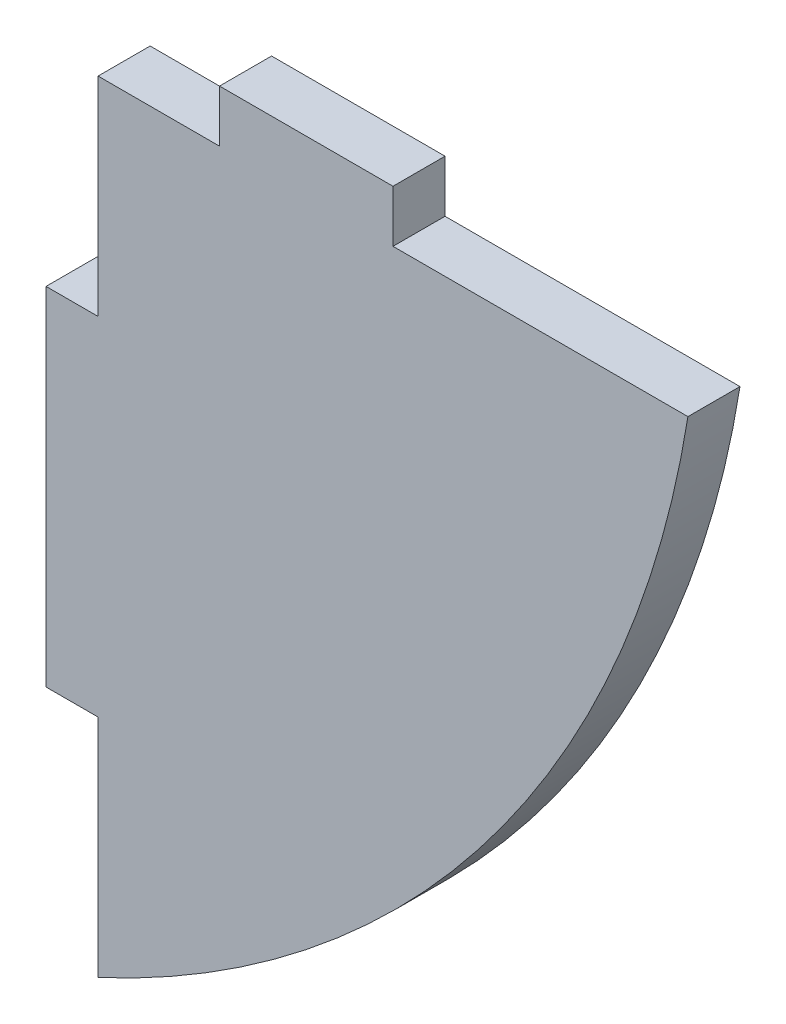
SolidWorks part; units mm, degrees
ref_plane "前视基准面" through (0, 0, 0) normal (0, 0, 1) x (1, 0, 0)
ref_plane "上视基准面" through (0, 0, 0) normal (0, 1, 0) x (1, 0, 0)
ref_plane "右视基准面" through (0, 0, 0) normal (1, 0, 0) x (0, 0, -1)
sketch "草图2" plane through (0, 0, 0) normal (0, 0, 1) x (1, 0, 0)
  line L0 (0, 45) -> (0, 33)
  line L1 (0, -55) -> (0, 55) construction
  line L2 (0, 45) -> (7, 45)
  line L3 (7, 45) -> (7, 48)
  line L4 (7, 48) -> (17, 48)
  line L5 (17, 48) -> (17, 45)
  line L6 (0, 33) -> (-3, 33)
  line L7 (-3, 33) -> (-3, 13)
  line L8 (-3, 13) -> (0, 13)
  line L9 (0, 13) -> (0, 0)
  line L10 (17, 45) -> (34, 45)
  arc A0 (34, 45) -> (0, 0) centre (-25.255, 54.426) cw
  dimension "D3" = 3
  dimension "D1" = 34
  dimension "D2" = 45
  dimension "D4" = 10
  dimension "D5" = 7
  dimension "D6" = 3
  dimension "D7" = 12
  dimension "D8" = 20
extrude "凸台-拉伸1" add sketch "草图2" along normal mid plane 3
